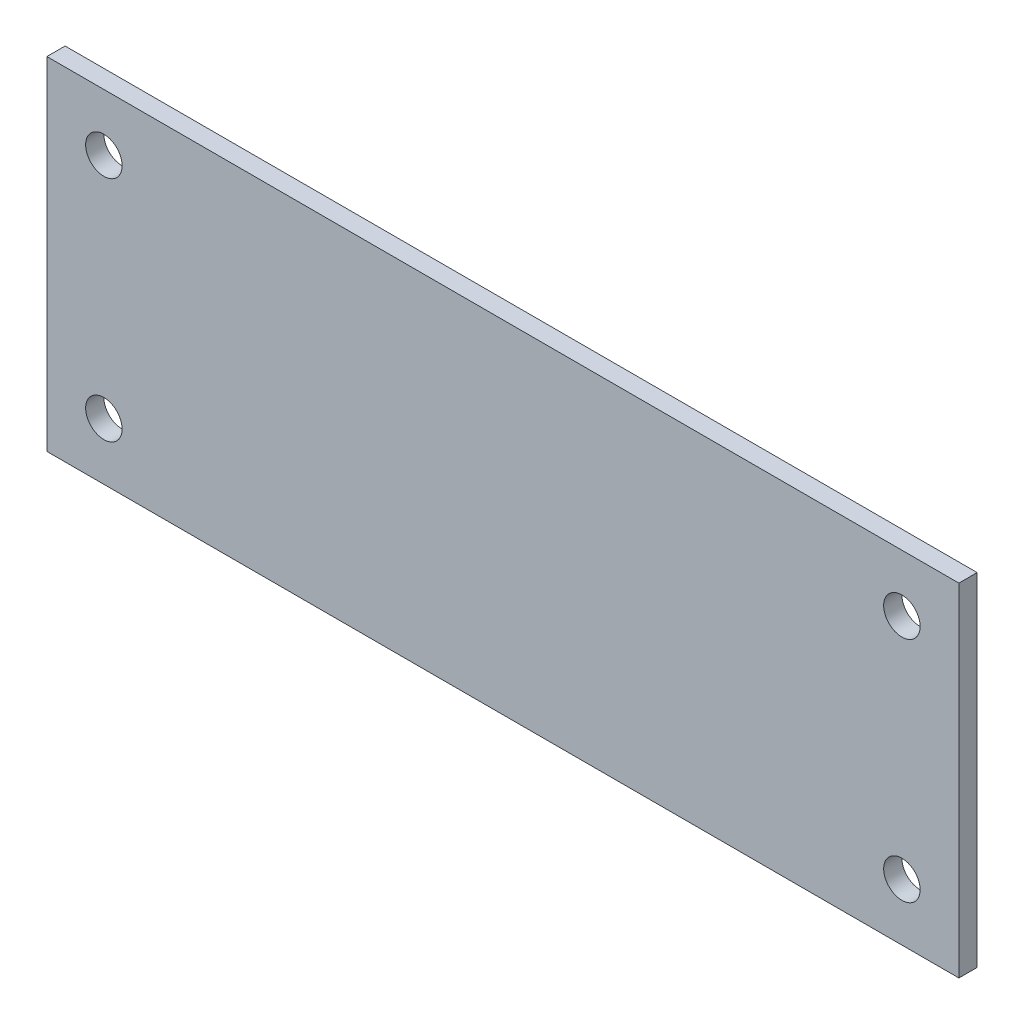
SolidWorks part; units mm, degrees
ref_plane "Front Plane" through (0, 0, 0) normal (0, 0, 1) x (1, 0, 0)
ref_plane "Top Plane" through (0, 0, 0) normal (0, 1, 0) x (1, 0, 0)
ref_plane "Right Plane" through (0, 0, 0) normal (1, 0, 0) x (0, 0, -1)
sketch "Esquisse1" plane through (0, 0, 0) normal (0, 0, 1) x (1, 0, 0)
  line L1 (-40, 15) -> (40, 15)
  line L2 (-40, 15) -> (-40, -15)
  line L3 (-40, -15) -> (40, -15)
  line L4 (40, 15) -> (40, -15)
  circle A0 centre (-35, 10) radius 1.6
  circle A1 centre (35, 10) radius 1.6
  circle A2 centre (35, -10) radius 1.6
  circle A3 centre (-35, -10) radius 1.6
  point P4 (0, -15)
  point P5 (40, 0)
  point P15 (0, 0)
  point P16 (0, 0)
  point P17 (-33.9872, 15)
  point P18 (0, 0)
  point P19 (0, 0)
  point P20 (0, 0)
  dimension "D3" = 3.2
  dimension "D1" = 80
  dimension "D2" = 30
  dimension "D4" = 5
  dimension "D5" = 5
  dimension "D6" = 5
  dimension "D7" = 5
extrude "Boss.-Extru.1" add sketch "Esquisse1" along normal blind 1.6
